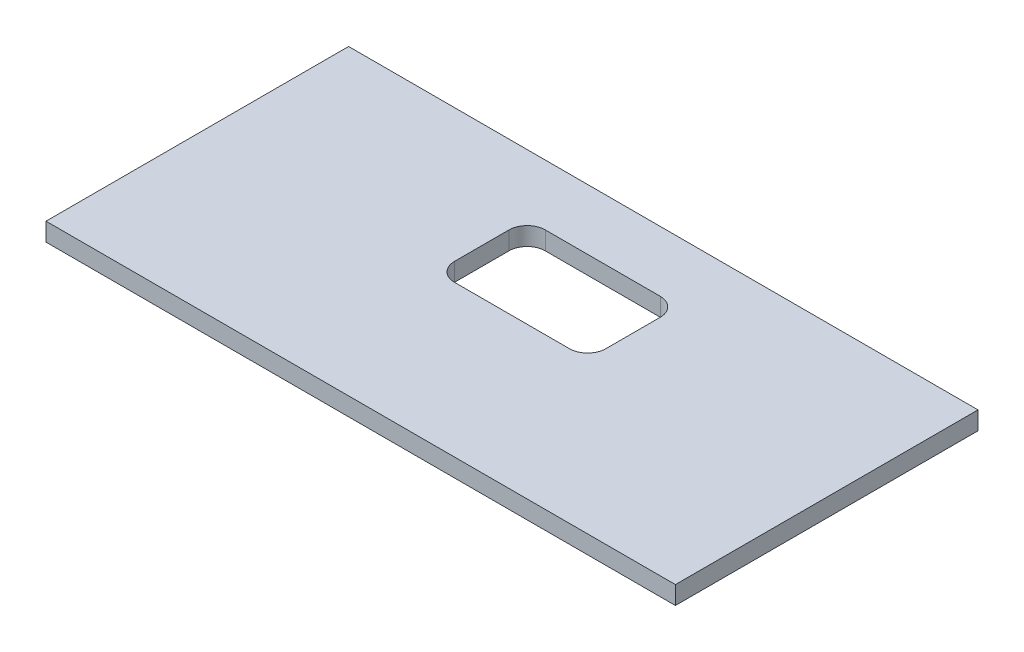
SolidWorks part; units mm, degrees
ref_plane "Ön Düzlem" through (0, 0, 0) normal (0, 0, 1) x (1, 0, 0)
ref_plane "Üst Düzlem" through (0, 0, 0) normal (0, 1, 0) x (1, 0, 0)
ref_plane "Sağ Düzlem" through (0, 0, 0) normal (1, 0, 0) x (0, 0, -1)
sketch "Çizim1" plane through (0, 0, 0) normal (0, 1, 0) x (1, 0, 0)
  line L1 (0, 0) -> (104, 0)
  line L2 (0, 0) -> (0, -50)
  line L3 (0, -50) -> (104, -50)
  line L4 (104, 0) -> (104, -50)
  line L5 (42.5, -10) -> (61.5, -10)
  line L6 (39.5, -13) -> (39.5, -22)
  line L7 (42.5, -25) -> (61.5, -25)
  line L8 (64.5, -13) -> (64.5, -22)
  arc A0 (61.5, -10) -> (64.5, -13) centre (61.5, -13) cw
  arc A1 (61.5, -25) -> (64.5, -22) centre (61.5, -22) ccw
  arc A2 (39.5, -22) -> (42.5, -25) centre (42.5, -22) ccw
  arc A3 (42.5, -10) -> (39.5, -13) centre (42.5, -13) ccw
  point P9 (52, 0)
  point P10 (52, -10)
  point P15 (64.5, -25)
  point P18 (39.5, -25)
  point P21 (39.5, -10)
  dimension "D6" = 3
  dimension "D1" = 104
  dimension "D2" = 50
  dimension "D3" = 25
  dimension "D4" = 15
  dimension "D5" = 25
extrude "Yükseklik-Ekstrüzyon1" add sketch "Çizim1" along normal blind 3
